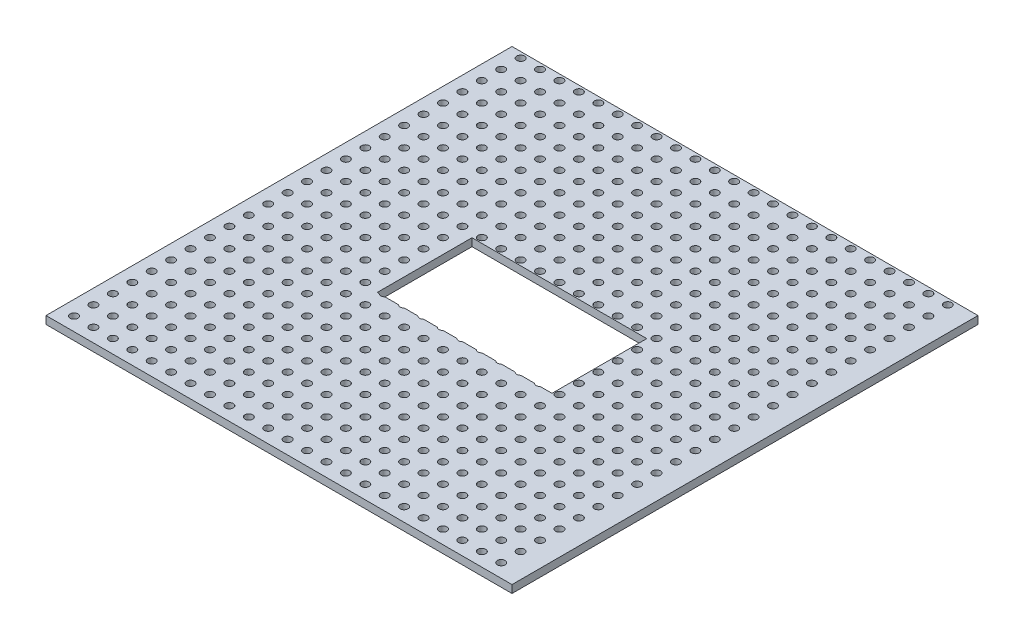
SolidWorks part; units mm, degrees
ref_plane "Front Plane" through (0, 0, 0) normal (0, 0, 1) x (1, 0, 0)
ref_plane "Top Plane" through (0, 0, 0) normal (0, 1, 0) x (1, 0, 0)
ref_plane "Right Plane" through (0, 0, 0) normal (1, 0, 0) x (0, 0, -1)
sketch "Sketch1" plane through (0, 0, 0) normal (0, 1, 0) x (1, 0, 0)
  line L0 (-42.6482, 0) -> (-42.6482, 60)
  line L1 (-42.6482, 60) -> (17.3518, 60)
  line L2 (17.3518, 60) -> (17.3518, 0)
  line L3 (17.3518, 0) -> (-42.6482, 0)
  line L5 (-1.3982, 23.9) -> (-23.8982, 23.9)
  line L6 (-1.3982, 23.9) -> (-1.3982, 36.1)
  line L7 (-1.3982, 36.1) -> (-23.8982, 36.1)
  line L8 (-23.8982, 23.9) -> (-23.8982, 36.1)
  line L9 (-1.3982, 23.9) -> (-23.8982, 36.1) construction
  line L10 (-1.3982, 36.1) -> (-23.8982, 23.9) construction
  point P0 (-12.6482, 30)
  dimension "D1" = 60
  dimension "D2" = 60
  dimension "D3" = 30
  dimension "D4" = 30
  dimension "D5" = 22.5
  dimension "D6" = 12.2
extrude "Boss-Extrude1" add sketch "Sketch1" along normal blind 1
sketch "Sketch2" plane through (0, 1, 0) normal (0, 1, 0) x (1, 0, 0)
  circle A0 centre (14.218, 59.2445) radius 0.5
  circle A1 centre (11.718, 59.2445) radius 0.5
  circle A2 centre (9.218, 59.2445) radius 0.5
  circle A3 centre (6.718, 59.2445) radius 0.5
  circle A4 centre (4.218, 59.2445) radius 0.5
  circle A5 centre (1.718, 59.2445) radius 0.5
  circle A6 centre (-0.782, 59.2445) radius 0.5
  circle A7 centre (-3.282, 59.2445) radius 0.5
  circle A8 centre (-5.782, 59.2445) radius 0.5
  circle A9 centre (-8.282, 59.2445) radius 0.5
  circle A10 centre (-10.782, 59.2445) radius 0.5
  circle A11 centre (-13.282, 59.2445) radius 0.5
  circle A12 centre (-15.782, 59.2445) radius 0.5
  circle A13 centre (-18.282, 59.2445) radius 0.5
  circle A14 centre (-20.782, 59.2445) radius 0.5
  circle A15 centre (-23.282, 59.2445) radius 0.5
  circle A16 centre (-25.782, 59.2445) radius 0.5
  circle A17 centre (-28.282, 59.2445) radius 0.5
  circle A18 centre (-30.782, 59.2445) radius 0.5
  circle A19 centre (-33.282, 59.2445) radius 0.5
  circle A20 centre (-35.782, 59.2445) radius 0.5
  circle A21 centre (-38.282, 59.2445) radius 0.5
  circle A22 centre (-40.782, 59.2445) radius 0.5
  circle A23 centre (-43.282, 59.2445) radius 0.5
  circle A24 centre (11.718, 56.7445) radius 0.5
  circle A25 centre (9.218, 56.7445) radius 0.5
  circle A26 centre (6.718, 56.7445) radius 0.5
  circle A27 centre (4.218, 56.7445) radius 0.5
  circle A28 centre (1.718, 56.7445) radius 0.5
  circle A29 centre (-0.782, 56.7445) radius 0.5
  circle A30 centre (-3.282, 56.7445) radius 0.5
  circle A31 centre (-5.782, 56.7445) radius 0.5
  circle A32 centre (-8.282, 56.7445) radius 0.5
  circle A33 centre (-10.782, 56.7445) radius 0.5
  circle A34 centre (-13.282, 56.7445) radius 0.5
  circle A35 centre (-15.782, 56.7445) radius 0.5
  circle A36 centre (-18.282, 56.7445) radius 0.5
  circle A37 centre (-20.782, 56.7445) radius 0.5
  circle A38 centre (-23.282, 56.7445) radius 0.5
  circle A39 centre (-25.782, 56.7445) radius 0.5
  circle A40 centre (-28.282, 56.7445) radius 0.5
  circle A41 centre (-30.782, 56.7445) radius 0.5
  circle A42 centre (-33.282, 56.7445) radius 0.5
  circle A43 centre (-35.782, 56.7445) radius 0.5
  circle A44 centre (-38.282, 56.7445) radius 0.5
  circle A45 centre (-40.782, 56.7445) radius 0.5
  circle A46 centre (-43.282, 56.7445) radius 0.5
  circle A47 centre (11.718, 54.2445) radius 0.5
  circle A48 centre (9.218, 54.2445) radius 0.5
  circle A49 centre (6.718, 54.2445) radius 0.5
  circle A50 centre (4.218, 54.2445) radius 0.5
  circle A51 centre (1.718, 54.2445) radius 0.5
  circle A52 centre (-0.782, 54.2445) radius 0.5
  circle A53 centre (-3.282, 54.2445) radius 0.5
  circle A54 centre (-5.782, 54.2445) radius 0.5
  circle A55 centre (-8.282, 54.2445) radius 0.5
  circle A56 centre (-10.782, 54.2445) radius 0.5
  circle A57 centre (-13.282, 54.2445) radius 0.5
  circle A58 centre (-15.782, 54.2445) radius 0.5
  circle A59 centre (-18.282, 54.2445) radius 0.5
  circle A60 centre (-20.782, 54.2445) radius 0.5
  circle A61 centre (-23.282, 54.2445) radius 0.5
  circle A62 centre (-25.782, 54.2445) radius 0.5
  circle A63 centre (-28.282, 54.2445) radius 0.5
  circle A64 centre (-30.782, 54.2445) radius 0.5
  circle A65 centre (-33.282, 54.2445) radius 0.5
  circle A66 centre (-35.782, 54.2445) radius 0.5
  circle A67 centre (-38.282, 54.2445) radius 0.5
  circle A68 centre (-40.782, 54.2445) radius 0.5
  circle A69 centre (-43.282, 54.2445) radius 0.5
  circle A70 centre (11.718, 51.7445) radius 0.5
  circle A71 centre (9.218, 51.7445) radius 0.5
  circle A72 centre (6.718, 51.7445) radius 0.5
  circle A73 centre (4.218, 51.7445) radius 0.5
  circle A74 centre (1.718, 51.7445) radius 0.5
  circle A75 centre (-0.782, 51.7445) radius 0.5
  circle A76 centre (-3.282, 51.7445) radius 0.5
  circle A77 centre (-5.782, 51.7445) radius 0.5
  circle A78 centre (-8.282, 51.7445) radius 0.5
  circle A79 centre (-10.782, 51.7445) radius 0.5
  circle A80 centre (-13.282, 51.7445) radius 0.5
  circle A81 centre (-15.782, 51.7445) radius 0.5
  circle A82 centre (-18.282, 51.7445) radius 0.5
  circle A83 centre (-20.782, 51.7445) radius 0.5
  circle A84 centre (-23.282, 51.7445) radius 0.5
  circle A85 centre (-25.782, 51.7445) radius 0.5
  circle A86 centre (-28.282, 51.7445) radius 0.5
  circle A87 centre (-30.782, 51.7445) radius 0.5
  circle A88 centre (-33.282, 51.7445) radius 0.5
  circle A89 centre (-35.782, 51.7445) radius 0.5
  circle A90 centre (-38.282, 51.7445) radius 0.5
  circle A91 centre (-40.782, 51.7445) radius 0.5
  circle A92 centre (-43.282, 51.7445) radius 0.5
  circle A93 centre (11.718, 49.2445) radius 0.5
  circle A94 centre (9.218, 49.2445) radius 0.5
  circle A95 centre (6.718, 49.2445) radius 0.5
  circle A96 centre (4.218, 49.2445) radius 0.5
  circle A97 centre (1.718, 49.2445) radius 0.5
  circle A98 centre (-0.782, 49.2445) radius 0.5
  circle A99 centre (-3.282, 49.2445) radius 0.5
  circle A100 centre (-5.782, 49.2445) radius 0.5
  circle A101 centre (-8.282, 49.2445) radius 0.5
  circle A102 centre (-10.782, 49.2445) radius 0.5
  circle A103 centre (-13.282, 49.2445) radius 0.5
  circle A104 centre (-15.782, 49.2445) radius 0.5
  circle A105 centre (-18.282, 49.2445) radius 0.5
  circle A106 centre (-20.782, 49.2445) radius 0.5
  circle A107 centre (-23.282, 49.2445) radius 0.5
  circle A108 centre (-25.782, 49.2445) radius 0.5
  circle A109 centre (-28.282, 49.2445) radius 0.5
  circle A110 centre (-30.782, 49.2445) radius 0.5
  circle A111 centre (-33.282, 49.2445) radius 0.5
  circle A112 centre (-35.782, 49.2445) radius 0.5
  circle A113 centre (-38.282, 49.2445) radius 0.5
  circle A114 centre (-40.782, 49.2445) radius 0.5
  circle A115 centre (-43.282, 49.2445) radius 0.5
  circle A116 centre (11.718, 46.7445) radius 0.5
  circle A117 centre (9.218, 46.7445) radius 0.5
  circle A118 centre (6.718, 46.7445) radius 0.5
  circle A119 centre (4.218, 46.7445) radius 0.5
  circle A120 centre (1.718, 46.7445) radius 0.5
  circle A121 centre (-0.782, 46.7445) radius 0.5
  circle A122 centre (-3.282, 46.7445) radius 0.5
  circle A123 centre (-5.782, 46.7445) radius 0.5
  circle A124 centre (-8.282, 46.7445) radius 0.5
  circle A125 centre (-10.782, 46.7445) radius 0.5
  circle A126 centre (-13.282, 46.7445) radius 0.5
  circle A127 centre (-15.782, 46.7445) radius 0.5
  circle A128 centre (-18.282, 46.7445) radius 0.5
  circle A129 centre (-20.782, 46.7445) radius 0.5
  circle A130 centre (-23.282, 46.7445) radius 0.5
  circle A131 centre (-25.782, 46.7445) radius 0.5
  circle A132 centre (-28.282, 46.7445) radius 0.5
  circle A133 centre (-30.782, 46.7445) radius 0.5
  circle A134 centre (-33.282, 46.7445) radius 0.5
  circle A135 centre (-35.782, 46.7445) radius 0.5
  circle A136 centre (-38.282, 46.7445) radius 0.5
  circle A137 centre (-40.782, 46.7445) radius 0.5
  circle A138 centre (-43.282, 46.7445) radius 0.5
  circle A139 centre (11.718, 44.2445) radius 0.5
  circle A140 centre (9.218, 44.2445) radius 0.5
  circle A141 centre (6.718, 44.2445) radius 0.5
  circle A142 centre (4.218, 44.2445) radius 0.5
  circle A143 centre (1.718, 44.2445) radius 0.5
  circle A144 centre (-0.782, 44.2445) radius 0.5
  circle A145 centre (-3.282, 44.2445) radius 0.5
  circle A146 centre (-5.782, 44.2445) radius 0.5
  circle A147 centre (-8.282, 44.2445) radius 0.5
  circle A148 centre (-10.782, 44.2445) radius 0.5
  circle A149 centre (-13.282, 44.2445) radius 0.5
  circle A150 centre (-15.782, 44.2445) radius 0.5
  circle A151 centre (-18.282, 44.2445) radius 0.5
  circle A152 centre (-20.782, 44.2445) radius 0.5
  circle A153 centre (-23.282, 44.2445) radius 0.5
  circle A154 centre (-25.782, 44.2445) radius 0.5
  circle A155 centre (-28.282, 44.2445) radius 0.5
  circle A156 centre (-30.782, 44.2445) radius 0.5
  circle A157 centre (-33.282, 44.2445) radius 0.5
  circle A158 centre (-35.782, 44.2445) radius 0.5
  circle A159 centre (-38.282, 44.2445) radius 0.5
  circle A160 centre (-40.782, 44.2445) radius 0.5
  circle A161 centre (-43.282, 44.2445) radius 0.5
  circle A162 centre (11.718, 41.7445) radius 0.5
  circle A163 centre (9.218, 41.7445) radius 0.5
  circle A164 centre (6.718, 41.7445) radius 0.5
  circle A165 centre (4.218, 41.7445) radius 0.5
  circle A166 centre (1.718, 41.7445) radius 0.5
  circle A167 centre (-0.782, 41.7445) radius 0.5
  circle A168 centre (-3.282, 41.7445) radius 0.5
  circle A169 centre (-5.782, 41.7445) radius 0.5
  circle A170 centre (-8.282, 41.7445) radius 0.5
  circle A171 centre (-10.782, 41.7445) radius 0.5
  circle A172 centre (-13.282, 41.7445) radius 0.5
  circle A173 centre (-15.782, 41.7445) radius 0.5
  circle A174 centre (-18.282, 41.7445) radius 0.5
  circle A175 centre (-20.782, 41.7445) radius 0.5
  circle A176 centre (-23.282, 41.7445) radius 0.5
  circle A177 centre (-25.782, 41.7445) radius 0.5
  circle A178 centre (-28.282, 41.7445) radius 0.5
  circle A179 centre (-30.782, 41.7445) radius 0.5
  circle A180 centre (-33.282, 41.7445) radius 0.5
  circle A181 centre (-35.782, 41.7445) radius 0.5
  circle A182 centre (-38.282, 41.7445) radius 0.5
  circle A183 centre (-40.782, 41.7445) radius 0.5
  circle A184 centre (-43.282, 41.7445) radius 0.5
  circle A185 centre (11.718, 39.2445) radius 0.5
  circle A186 centre (9.218, 39.2445) radius 0.5
  circle A187 centre (6.718, 39.2445) radius 0.5
  circle A188 centre (4.218, 39.2445) radius 0.5
  circle A189 centre (1.718, 39.2445) radius 0.5
  circle A190 centre (-0.782, 39.2445) radius 0.5
  circle A191 centre (-3.282, 39.2445) radius 0.5
  circle A192 centre (-5.782, 39.2445) radius 0.5
  circle A193 centre (-8.282, 39.2445) radius 0.5
  circle A194 centre (-10.782, 39.2445) radius 0.5
  circle A195 centre (-13.282, 39.2445) radius 0.5
  circle A196 centre (-15.782, 39.2445) radius 0.5
  circle A197 centre (-18.282, 39.2445) radius 0.5
  circle A198 centre (-20.782, 39.2445) radius 0.5
  circle A199 centre (-23.282, 39.2445) radius 0.5
  circle A200 centre (-25.782, 39.2445) radius 0.5
  circle A201 centre (-28.282, 39.2445) radius 0.5
  circle A202 centre (-30.782, 39.2445) radius 0.5
  circle A203 centre (-33.282, 39.2445) radius 0.5
  circle A204 centre (-35.782, 39.2445) radius 0.5
  circle A205 centre (-38.282, 39.2445) radius 0.5
  circle A206 centre (-40.782, 39.2445) radius 0.5
  circle A207 centre (-43.282, 39.2445) radius 0.5
  circle A208 centre (11.718, 36.7445) radius 0.5
  circle A209 centre (9.218, 36.7445) radius 0.5
  circle A210 centre (6.718, 36.7445) radius 0.5
  circle A211 centre (4.218, 36.7445) radius 0.5
  circle A212 centre (1.718, 36.7445) radius 0.5
  circle A213 centre (-0.782, 36.7445) radius 0.5
  circle A214 centre (-3.282, 36.7445) radius 0.5
  circle A215 centre (-5.782, 36.7445) radius 0.5
  circle A216 centre (-8.282, 36.7445) radius 0.5
  circle A217 centre (-10.782, 36.7445) radius 0.5
  circle A218 centre (-13.282, 36.7445) radius 0.5
  circle A219 centre (-15.782, 36.7445) radius 0.5
  circle A220 centre (-18.282, 36.7445) radius 0.5
  circle A221 centre (-20.782, 36.7445) radius 0.5
  circle A222 centre (-23.282, 36.7445) radius 0.5
  circle A223 centre (-25.782, 36.7445) radius 0.5
  circle A224 centre (-28.282, 36.7445) radius 0.5
  circle A225 centre (-30.782, 36.7445) radius 0.5
  circle A226 centre (-33.282, 36.7445) radius 0.5
  circle A227 centre (-35.782, 36.7445) radius 0.5
  circle A228 centre (-38.282, 36.7445) radius 0.5
  circle A229 centre (-40.782, 36.7445) radius 0.5
  circle A230 centre (-43.282, 36.7445) radius 0.5
  circle A231 centre (11.718, 34.2445) radius 0.5
  circle A232 centre (9.218, 34.2445) radius 0.5
  circle A233 centre (6.718, 34.2445) radius 0.5
  circle A234 centre (4.218, 34.2445) radius 0.5
  circle A235 centre (1.718, 34.2445) radius 0.5
  circle A236 centre (-0.782, 34.2445) radius 0.5
  circle A237 centre (-3.282, 34.2445) radius 0.5
  circle A238 centre (-5.782, 34.2445) radius 0.5
  circle A239 centre (-8.282, 34.2445) radius 0.5
  circle A240 centre (-10.782, 34.2445) radius 0.5
  circle A241 centre (-13.282, 34.2445) radius 0.5
  circle A242 centre (-15.782, 34.2445) radius 0.5
  circle A243 centre (-18.282, 34.2445) radius 0.5
  circle A244 centre (-20.782, 34.2445) radius 0.5
  circle A245 centre (-23.282, 34.2445) radius 0.5
  circle A246 centre (-25.782, 34.2445) radius 0.5
  circle A247 centre (-28.282, 34.2445) radius 0.5
  circle A248 centre (-30.782, 34.2445) radius 0.5
  circle A249 centre (-33.282, 34.2445) radius 0.5
  circle A250 centre (-35.782, 34.2445) radius 0.5
  circle A251 centre (-38.282, 34.2445) radius 0.5
  circle A252 centre (-40.782, 34.2445) radius 0.5
  circle A253 centre (-43.282, 34.2445) radius 0.5
  circle A254 centre (11.718, 31.7445) radius 0.5
  circle A255 centre (9.218, 31.7445) radius 0.5
  circle A256 centre (6.718, 31.7445) radius 0.5
  circle A257 centre (4.218, 31.7445) radius 0.5
  circle A258 centre (1.718, 31.7445) radius 0.5
  circle A259 centre (-0.782, 31.7445) radius 0.5
  circle A260 centre (-3.282, 31.7445) radius 0.5
  circle A261 centre (-5.782, 31.7445) radius 0.5
  circle A262 centre (-8.282, 31.7445) radius 0.5
  circle A263 centre (-10.782, 31.7445) radius 0.5
  circle A264 centre (-13.282, 31.7445) radius 0.5
  circle A265 centre (-15.782, 31.7445) radius 0.5
  circle A266 centre (-18.282, 31.7445) radius 0.5
  circle A267 centre (-20.782, 31.7445) radius 0.5
  circle A268 centre (-23.282, 31.7445) radius 0.5
  circle A269 centre (-25.782, 31.7445) radius 0.5
  circle A270 centre (-28.282, 31.7445) radius 0.5
  circle A271 centre (-30.782, 31.7445) radius 0.5
  circle A272 centre (-33.282, 31.7445) radius 0.5
  circle A273 centre (-35.782, 31.7445) radius 0.5
  circle A274 centre (-38.282, 31.7445) radius 0.5
  circle A275 centre (-40.782, 31.7445) radius 0.5
  circle A276 centre (-43.282, 31.7445) radius 0.5
  circle A277 centre (11.718, 29.2445) radius 0.5
  circle A278 centre (9.218, 29.2445) radius 0.5
  circle A279 centre (6.718, 29.2445) radius 0.5
  circle A280 centre (4.218, 29.2445) radius 0.5
  circle A281 centre (1.718, 29.2445) radius 0.5
  circle A282 centre (-0.782, 29.2445) radius 0.5
  circle A283 centre (-3.282, 29.2445) radius 0.5
  circle A284 centre (-5.782, 29.2445) radius 0.5
  circle A285 centre (-8.282, 29.2445) radius 0.5
  circle A286 centre (-10.782, 29.2445) radius 0.5
  circle A287 centre (-13.282, 29.2445) radius 0.5
  circle A288 centre (-15.782, 29.2445) radius 0.5
  circle A289 centre (-18.282, 29.2445) radius 0.5
  circle A290 centre (-20.782, 29.2445) radius 0.5
  circle A291 centre (-23.282, 29.2445) radius 0.5
  circle A292 centre (-25.782, 29.2445) radius 0.5
  circle A293 centre (-28.282, 29.2445) radius 0.5
  circle A294 centre (-30.782, 29.2445) radius 0.5
  circle A295 centre (-33.282, 29.2445) radius 0.5
  circle A296 centre (-35.782, 29.2445) radius 0.5
  circle A297 centre (-38.282, 29.2445) radius 0.5
  circle A298 centre (-40.782, 29.2445) radius 0.5
  circle A299 centre (-43.282, 29.2445) radius 0.5
  circle A300 centre (11.718, 26.7445) radius 0.5
  circle A301 centre (9.218, 26.7445) radius 0.5
  circle A302 centre (6.718, 26.7445) radius 0.5
  circle A303 centre (4.218, 26.7445) radius 0.5
  circle A304 centre (1.718, 26.7445) radius 0.5
  circle A305 centre (-0.782, 26.7445) radius 0.5
  circle A306 centre (-3.282, 26.7445) radius 0.5
  circle A307 centre (-5.782, 26.7445) radius 0.5
  circle A308 centre (-8.282, 26.7445) radius 0.5
  circle A309 centre (-10.782, 26.7445) radius 0.5
  circle A310 centre (-13.282, 26.7445) radius 0.5
  circle A311 centre (-15.782, 26.7445) radius 0.5
  circle A312 centre (-18.282, 26.7445) radius 0.5
  circle A313 centre (-20.782, 26.7445) radius 0.5
  circle A314 centre (-23.282, 26.7445) radius 0.5
  circle A315 centre (-25.782, 26.7445) radius 0.5
  circle A316 centre (-28.282, 26.7445) radius 0.5
  circle A317 centre (-30.782, 26.7445) radius 0.5
  circle A318 centre (-33.282, 26.7445) radius 0.5
  circle A319 centre (-35.782, 26.7445) radius 0.5
  circle A320 centre (-38.282, 26.7445) radius 0.5
  circle A321 centre (-40.782, 26.7445) radius 0.5
  circle A322 centre (-43.282, 26.7445) radius 0.5
  circle A323 centre (11.718, 24.2445) radius 0.5
  circle A324 centre (9.218, 24.2445) radius 0.5
  circle A325 centre (6.718, 24.2445) radius 0.5
  circle A326 centre (4.218, 24.2445) radius 0.5
  circle A327 centre (1.718, 24.2445) radius 0.5
  circle A328 centre (-0.782, 24.2445) radius 0.5
  circle A329 centre (-3.282, 24.2445) radius 0.5
  circle A330 centre (-5.782, 24.2445) radius 0.5
  circle A331 centre (-8.282, 24.2445) radius 0.5
  circle A332 centre (-10.782, 24.2445) radius 0.5
  circle A333 centre (-13.282, 24.2445) radius 0.5
  circle A334 centre (-15.782, 24.2445) radius 0.5
  circle A335 centre (-18.282, 24.2445) radius 0.5
  circle A336 centre (-20.782, 24.2445) radius 0.5
  circle A337 centre (-23.282, 24.2445) radius 0.5
  circle A338 centre (-25.782, 24.2445) radius 0.5
  circle A339 centre (-28.282, 24.2445) radius 0.5
  circle A340 centre (-30.782, 24.2445) radius 0.5
  circle A341 centre (-33.282, 24.2445) radius 0.5
  circle A342 centre (-35.782, 24.2445) radius 0.5
  circle A343 centre (-38.282, 24.2445) radius 0.5
  circle A344 centre (-40.782, 24.2445) radius 0.5
  circle A345 centre (-43.282, 24.2445) radius 0.5
  circle A346 centre (11.718, 21.7445) radius 0.5
  circle A347 centre (9.218, 21.7445) radius 0.5
  circle A348 centre (6.718, 21.7445) radius 0.5
  circle A349 centre (4.218, 21.7445) radius 0.5
  circle A350 centre (1.718, 21.7445) radius 0.5
  circle A351 centre (-0.782, 21.7445) radius 0.5
  circle A352 centre (-3.282, 21.7445) radius 0.5
  circle A353 centre (-5.782, 21.7445) radius 0.5
  circle A354 centre (-8.282, 21.7445) radius 0.5
  circle A355 centre (-10.782, 21.7445) radius 0.5
  circle A356 centre (-13.282, 21.7445) radius 0.5
  circle A357 centre (-15.782, 21.7445) radius 0.5
  circle A358 centre (-18.282, 21.7445) radius 0.5
  circle A359 centre (-20.782, 21.7445) radius 0.5
  circle A360 centre (-23.282, 21.7445) radius 0.5
  circle A361 centre (-25.782, 21.7445) radius 0.5
  circle A362 centre (-28.282, 21.7445) radius 0.5
  circle A363 centre (-30.782, 21.7445) radius 0.5
  circle A364 centre (-33.282, 21.7445) radius 0.5
  circle A365 centre (-35.782, 21.7445) radius 0.5
  circle A366 centre (-38.282, 21.7445) radius 0.5
  circle A367 centre (-40.782, 21.7445) radius 0.5
  circle A368 centre (-43.282, 21.7445) radius 0.5
  circle A369 centre (11.718, 19.2445) radius 0.5
  circle A370 centre (9.218, 19.2445) radius 0.5
  circle A371 centre (6.718, 19.2445) radius 0.5
  circle A372 centre (4.218, 19.2445) radius 0.5
  circle A373 centre (1.718, 19.2445) radius 0.5
  circle A374 centre (-0.782, 19.2445) radius 0.5
  circle A375 centre (-3.282, 19.2445) radius 0.5
  circle A376 centre (-5.782, 19.2445) radius 0.5
  circle A377 centre (-8.282, 19.2445) radius 0.5
  circle A378 centre (-10.782, 19.2445) radius 0.5
  circle A379 centre (-13.282, 19.2445) radius 0.5
  circle A380 centre (-15.782, 19.2445) radius 0.5
  circle A381 centre (-18.282, 19.2445) radius 0.5
  circle A382 centre (-20.782, 19.2445) radius 0.5
  circle A383 centre (-23.282, 19.2445) radius 0.5
  circle A384 centre (-25.782, 19.2445) radius 0.5
  circle A385 centre (-28.282, 19.2445) radius 0.5
  circle A386 centre (-30.782, 19.2445) radius 0.5
  circle A387 centre (-33.282, 19.2445) radius 0.5
  circle A388 centre (-35.782, 19.2445) radius 0.5
  circle A389 centre (-38.282, 19.2445) radius 0.5
  circle A390 centre (-40.782, 19.2445) radius 0.5
  circle A391 centre (-43.282, 19.2445) radius 0.5
  circle A392 centre (11.718, 16.7445) radius 0.5
  circle A393 centre (9.218, 16.7445) radius 0.5
  circle A394 centre (6.718, 16.7445) radius 0.5
  circle A395 centre (4.218, 16.7445) radius 0.5
  circle A396 centre (1.718, 16.7445) radius 0.5
  circle A397 centre (-0.782, 16.7445) radius 0.5
  circle A398 centre (-3.282, 16.7445) radius 0.5
  circle A399 centre (-5.782, 16.7445) radius 0.5
  circle A400 centre (-8.282, 16.7445) radius 0.5
  circle A401 centre (-10.782, 16.7445) radius 0.5
  circle A402 centre (-13.282, 16.7445) radius 0.5
  circle A403 centre (-15.782, 16.7445) radius 0.5
  circle A404 centre (-18.282, 16.7445) radius 0.5
  circle A405 centre (-20.782, 16.7445) radius 0.5
  circle A406 centre (-23.282, 16.7445) radius 0.5
  circle A407 centre (-25.782, 16.7445) radius 0.5
  circle A408 centre (-28.282, 16.7445) radius 0.5
  circle A409 centre (-30.782, 16.7445) radius 0.5
  circle A410 centre (-33.282, 16.7445) radius 0.5
  circle A411 centre (-35.782, 16.7445) radius 0.5
  circle A412 centre (-38.282, 16.7445) radius 0.5
  circle A413 centre (-40.782, 16.7445) radius 0.5
  circle A414 centre (-43.282, 16.7445) radius 0.5
  circle A415 centre (11.718, 14.2445) radius 0.5
  circle A416 centre (9.218, 14.2445) radius 0.5
  circle A417 centre (6.718, 14.2445) radius 0.5
  circle A418 centre (4.218, 14.2445) radius 0.5
  circle A419 centre (1.718, 14.2445) radius 0.5
  circle A420 centre (-0.782, 14.2445) radius 0.5
  circle A421 centre (-3.282, 14.2445) radius 0.5
  circle A422 centre (-5.782, 14.2445) radius 0.5
  circle A423 centre (-8.282, 14.2445) radius 0.5
  circle A424 centre (-10.782, 14.2445) radius 0.5
  circle A425 centre (-13.282, 14.2445) radius 0.5
  circle A426 centre (-15.782, 14.2445) radius 0.5
  circle A427 centre (-18.282, 14.2445) radius 0.5
  circle A428 centre (-20.782, 14.2445) radius 0.5
  circle A429 centre (-23.282, 14.2445) radius 0.5
  circle A430 centre (-25.782, 14.2445) radius 0.5
  circle A431 centre (-28.282, 14.2445) radius 0.5
  circle A432 centre (-30.782, 14.2445) radius 0.5
  circle A433 centre (-33.282, 14.2445) radius 0.5
  circle A434 centre (-35.782, 14.2445) radius 0.5
  circle A435 centre (-38.282, 14.2445) radius 0.5
  circle A436 centre (-40.782, 14.2445) radius 0.5
  circle A437 centre (-43.282, 14.2445) radius 0.5
  circle A438 centre (11.718, 11.7445) radius 0.5
  circle A439 centre (9.218, 11.7445) radius 0.5
  circle A440 centre (6.718, 11.7445) radius 0.5
  circle A441 centre (4.218, 11.7445) radius 0.5
  circle A442 centre (1.718, 11.7445) radius 0.5
  circle A443 centre (-0.782, 11.7445) radius 0.5
  circle A444 centre (-3.282, 11.7445) radius 0.5
  circle A445 centre (-5.782, 11.7445) radius 0.5
  circle A446 centre (-8.282, 11.7445) radius 0.5
  circle A447 centre (-10.782, 11.7445) radius 0.5
  circle A448 centre (-13.282, 11.7445) radius 0.5
  circle A449 centre (-15.782, 11.7445) radius 0.5
  circle A450 centre (-18.282, 11.7445) radius 0.5
  circle A451 centre (-20.782, 11.7445) radius 0.5
  circle A452 centre (-23.282, 11.7445) radius 0.5
  circle A453 centre (-25.782, 11.7445) radius 0.5
  circle A454 centre (-28.282, 11.7445) radius 0.5
  circle A455 centre (-30.782, 11.7445) radius 0.5
  circle A456 centre (-33.282, 11.7445) radius 0.5
  circle A457 centre (-35.782, 11.7445) radius 0.5
  circle A458 centre (-38.282, 11.7445) radius 0.5
  circle A459 centre (-40.782, 11.7445) radius 0.5
  circle A460 centre (-43.282, 11.7445) radius 0.5
  circle A461 centre (11.718, 9.2445) radius 0.5
  circle A462 centre (9.218, 9.2445) radius 0.5
  circle A463 centre (6.718, 9.2445) radius 0.5
  circle A464 centre (4.218, 9.2445) radius 0.5
  circle A465 centre (1.718, 9.2445) radius 0.5
  circle A466 centre (-0.782, 9.2445) radius 0.5
  circle A467 centre (-3.282, 9.2445) radius 0.5
  circle A468 centre (-5.782, 9.2445) radius 0.5
  circle A469 centre (-8.282, 9.2445) radius 0.5
  circle A470 centre (-10.782, 9.2445) radius 0.5
  circle A471 centre (-13.282, 9.2445) radius 0.5
  circle A472 centre (-15.782, 9.2445) radius 0.5
  circle A473 centre (-18.282, 9.2445) radius 0.5
  circle A474 centre (-20.782, 9.2445) radius 0.5
  circle A475 centre (-23.282, 9.2445) radius 0.5
  circle A476 centre (-25.782, 9.2445) radius 0.5
  circle A477 centre (-28.282, 9.2445) radius 0.5
  circle A478 centre (-30.782, 9.2445) radius 0.5
  circle A479 centre (-33.282, 9.2445) radius 0.5
  circle A480 centre (-35.782, 9.2445) radius 0.5
  circle A481 centre (-38.282, 9.2445) radius 0.5
  circle A482 centre (-40.782, 9.2445) radius 0.5
  circle A483 centre (-43.282, 9.2445) radius 0.5
  circle A484 centre (11.718, 6.7445) radius 0.5
  circle A485 centre (9.218, 6.7445) radius 0.5
  circle A486 centre (6.718, 6.7445) radius 0.5
  circle A487 centre (4.218, 6.7445) radius 0.5
  circle A488 centre (1.718, 6.7445) radius 0.5
  circle A489 centre (-0.782, 6.7445) radius 0.5
  circle A490 centre (-3.282, 6.7445) radius 0.5
  circle A491 centre (-5.782, 6.7445) radius 0.5
  circle A492 centre (-8.282, 6.7445) radius 0.5
  circle A493 centre (-10.782, 6.7445) radius 0.5
  circle A494 centre (-13.282, 6.7445) radius 0.5
  circle A495 centre (-15.782, 6.7445) radius 0.5
  circle A496 centre (-18.282, 6.7445) radius 0.5
  circle A497 centre (-20.782, 6.7445) radius 0.5
  circle A498 centre (-23.282, 6.7445) radius 0.5
  circle A499 centre (-25.782, 6.7445) radius 0.5
  circle A500 centre (-28.282, 6.7445) radius 0.5
  circle A501 centre (-30.782, 6.7445) radius 0.5
  circle A502 centre (-33.282, 6.7445) radius 0.5
  circle A503 centre (-35.782, 6.7445) radius 0.5
  circle A504 centre (-38.282, 6.7445) radius 0.5
  circle A505 centre (-40.782, 6.7445) radius 0.5
  circle A506 centre (-43.282, 6.7445) radius 0.5
  circle A507 centre (11.718, 4.2445) radius 0.5
  circle A508 centre (9.218, 4.2445) radius 0.5
  circle A509 centre (6.718, 4.2445) radius 0.5
  circle A510 centre (4.218, 4.2445) radius 0.5
  circle A511 centre (1.718, 4.2445) radius 0.5
  circle A512 centre (-0.782, 4.2445) radius 0.5
  circle A513 centre (-3.282, 4.2445) radius 0.5
  circle A514 centre (-5.782, 4.2445) radius 0.5
  circle A515 centre (-8.282, 4.2445) radius 0.5
  circle A516 centre (-10.782, 4.2445) radius 0.5
  circle A517 centre (-13.282, 4.2445) radius 0.5
  circle A518 centre (-15.782, 4.2445) radius 0.5
  circle A519 centre (-18.282, 4.2445) radius 0.5
  circle A520 centre (-20.782, 4.2445) radius 0.5
  circle A521 centre (-23.282, 4.2445) radius 0.5
  circle A522 centre (-25.782, 4.2445) radius 0.5
  circle A523 centre (-28.282, 4.2445) radius 0.5
  circle A524 centre (-30.782, 4.2445) radius 0.5
  circle A525 centre (-33.282, 4.2445) radius 0.5
  circle A526 centre (-35.782, 4.2445) radius 0.5
  circle A527 centre (-38.282, 4.2445) radius 0.5
  circle A528 centre (-40.782, 4.2445) radius 0.5
  circle A529 centre (-43.282, 4.2445) radius 0.5
  circle A530 centre (11.718, 1.7445) radius 0.5
  circle A531 centre (9.218, 1.7445) radius 0.5
  circle A532 centre (6.718, 1.7445) radius 0.5
  circle A533 centre (4.218, 1.7445) radius 0.5
  circle A534 centre (1.718, 1.7445) radius 0.5
  circle A535 centre (-0.782, 1.7445) radius 0.5
  circle A536 centre (-3.282, 1.7445) radius 0.5
  circle A537 centre (-5.782, 1.7445) radius 0.5
  circle A538 centre (-8.282, 1.7445) radius 0.5
  circle A539 centre (-10.782, 1.7445) radius 0.5
  circle A540 centre (-13.282, 1.7445) radius 0.5
  circle A541 centre (-15.782, 1.7445) radius 0.5
  circle A542 centre (-18.282, 1.7445) radius 0.5
  circle A543 centre (-20.782, 1.7445) radius 0.5
  circle A544 centre (-23.282, 1.7445) radius 0.5
  circle A545 centre (-25.782, 1.7445) radius 0.5
  circle A546 centre (-28.282, 1.7445) radius 0.5
  circle A547 centre (-30.782, 1.7445) radius 0.5
  circle A548 centre (-33.282, 1.7445) radius 0.5
  circle A549 centre (-35.782, 1.7445) radius 0.5
  circle A550 centre (-38.282, 1.7445) radius 0.5
  circle A551 centre (-40.782, 1.7445) radius 0.5
  circle A552 centre (-43.282, 1.7445) radius 0.5
  circle A553 centre (14.218, 56.7445) radius 0.5
  circle A554 centre (14.218, 54.2445) radius 0.5
  circle A555 centre (14.218, 51.7445) radius 0.5
  circle A556 centre (14.218, 49.2445) radius 0.5
  circle A557 centre (14.218, 46.7445) radius 0.5
  circle A558 centre (14.218, 44.2445) radius 0.5
  circle A559 centre (14.218, 41.7445) radius 0.5
  circle A560 centre (14.218, 39.2445) radius 0.5
  circle A561 centre (14.218, 36.7445) radius 0.5
  circle A562 centre (14.218, 34.2445) radius 0.5
  circle A563 centre (14.218, 31.7445) radius 0.5
  circle A564 centre (14.218, 29.2445) radius 0.5
  circle A565 centre (14.218, 26.7445) radius 0.5
  circle A566 centre (14.218, 24.2445) radius 0.5
  circle A567 centre (14.218, 21.7445) radius 0.5
  circle A568 centre (14.218, 19.2445) radius 0.5
  circle A569 centre (14.218, 16.7445) radius 0.5
  circle A570 centre (14.218, 14.2445) radius 0.5
  circle A571 centre (14.218, 11.7445) radius 0.5
  circle A572 centre (14.218, 9.2445) radius 0.5
  circle A573 centre (14.218, 6.7445) radius 0.5
  circle A574 centre (14.218, 4.2445) radius 0.5
  circle A575 centre (14.218, 1.7445) radius 0.5
  dimension "D1" = 1
  dimension "D2" = 24
extrude "Cut-Extrude1" cut sketch "Sketch2" against normal through all
